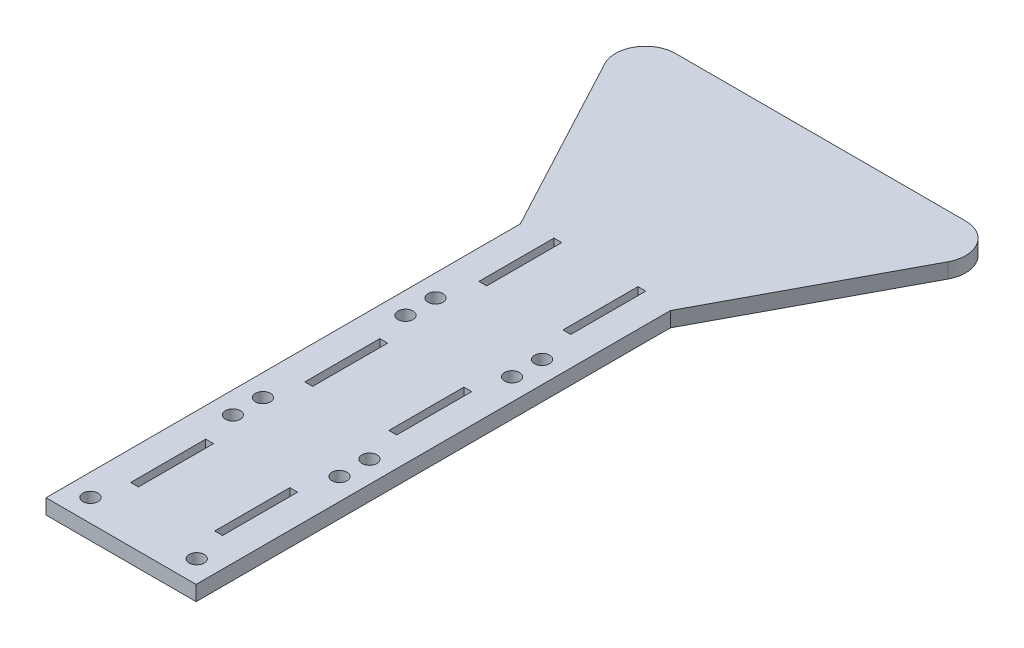
SolidWorks part; units mm, degrees
material "PC High Viscosity"
ref_plane "Front" through (0, 0, 0) normal (0, 0, 1) x (1, 0, 0)
ref_plane "Top" through (0, 0, 0) normal (0, 1, 0) x (1, 0, 0)
ref_plane "Right" through (0, 0, 0) normal (1, 0, 0) x (0, 0, -1)
sketch "Sketch1" plane through (0, 0, 0) normal (0, 1, 0) x (1, 0, 0)
  line L0 (-31.75, 0) -> (31.75, 0)
  line L1 (31.75, 0) -> (31.75, 200.66)
  line L2 (31.75, 200.66) -> (82.55, 295.91)
  line L3 (82.55, 295.91) -> (-82.55, 295.91)
  line L4 (-82.55, 295.91) -> (-31.75, 200.66)
  line L5 (-31.75, 200.66) -> (-31.75, 0)
  point P4 (0, 0)
  dimension "D1" = 63.5
  dimension "D2" = 200.66
  dimension "D3" = 95.25
  dimension "D4" = 165.1
extrude "Boss-Extrude1" add sketch "Sketch1" along normal blind 6.35
sketch "Sketch2" plane through (0, 6.35, 0) normal (0, 1, 0) x (1, 0, 0)
  line L0 (-19.3675, 199.39) -> (-19.3675, 173.99) construction
  line L1 (-19.3675, 173.99) -> (-16.1925, 173.99) construction
  line L2 (-16.1925, 173.99) -> (-16.1925, 199.39) construction
  line L3 (-16.1925, 199.39) -> (-19.3675, 199.39) construction
  line L4 (-19.3675, 125.73) -> (-19.3675, 100.33) construction
  line L5 (-19.3675, 100.33) -> (-16.1925, 100.33) construction
  line L6 (-16.1925, 100.33) -> (-16.1925, 125.73) construction
  line L7 (-16.1925, 125.73) -> (-19.3675, 125.73) construction
  line L12 (-19.3675, 52.07) -> (-19.3675, 26.67) construction
  line L13 (-19.3675, 26.67) -> (-16.1925, 26.67) construction
  line L14 (-16.1925, 26.67) -> (-16.1925, 52.07) construction
  line L15 (-16.1925, 52.07) -> (-19.3675, 52.07) construction
  line L20 (-19.3675, 199.39) -> (-19.3675, 173.99) construction
  line L21 (-19.3675, 173.99) -> (-16.1925, 173.99) construction
  line L22 (-16.1925, 173.99) -> (-16.1925, 199.39) construction
  line L23 (-16.1925, 199.39) -> (-19.3675, 199.39) construction
  line L24 (-19.3675, 125.73) -> (-19.3675, 100.33) construction
  line L25 (-19.3675, 100.33) -> (-16.1925, 100.33) construction
  line L26 (-16.1925, 100.33) -> (-16.1925, 125.73) construction
  line L27 (-16.1925, 125.73) -> (-19.3675, 125.73) construction
  line L32 (-19.3675, 52.07) -> (-19.3675, 26.67) construction
  line L33 (-19.3675, 26.67) -> (-16.1925, 26.67) construction
  line L34 (-16.1925, 26.67) -> (-16.1925, 52.07) construction
  line L35 (-16.1925, 52.07) -> (-19.3675, 52.07) construction
  line L36 (16.1925, 52.07) -> (16.1925, 26.67) construction
  line L37 (16.1925, 26.67) -> (19.3675, 26.67) construction
  line L38 (19.3675, 26.67) -> (19.3675, 52.07) construction
  line L39 (19.3675, 52.07) -> (16.1925, 52.07) construction
  line L44 (16.1925, 125.73) -> (16.1925, 100.33) construction
  line L45 (16.1925, 100.33) -> (19.3675, 100.33) construction
  line L46 (19.3675, 100.33) -> (19.3675, 125.73) construction
  line L47 (19.3675, 125.73) -> (16.1925, 125.73) construction
  line L48 (16.1925, 199.39) -> (16.1925, 173.99) construction
  line L49 (16.1925, 173.99) -> (19.3675, 173.99) construction
  line L50 (19.3675, 173.99) -> (19.3675, 199.39) construction
  line L51 (19.3675, 199.39) -> (16.1925, 199.39) construction
  line L56 (16.1925, 52.07) -> (16.1925, 26.67) construction
  line L57 (16.1925, 26.67) -> (19.3675, 26.67) construction
  line L58 (19.3675, 26.67) -> (19.3675, 52.07) construction
  line L59 (19.3675, 52.07) -> (16.1925, 52.07) construction
  line L60 (16.1925, 125.73) -> (16.1925, 100.33) construction
  line L61 (16.1925, 100.33) -> (19.3675, 100.33) construction
  line L62 (19.3675, 100.33) -> (19.3675, 125.73) construction
  line L63 (19.3675, 125.73) -> (16.1925, 125.73) construction
  line L68 (16.1925, 199.39) -> (16.1925, 173.99) construction
  line L69 (16.1925, 173.99) -> (19.3675, 173.99) construction
  line L70 (19.3675, 173.99) -> (19.3675, 199.39) construction
  line L71 (19.3675, 199.39) -> (16.1925, 199.39) construction
  line L72 (-19.431, 23.495) -> (-19.3675, 26.67) construction
  line L73 (-19.431, 23.495) -> (-16.129, 23.495)
  line L74 (-19.431, 23.495) -> (-19.431, 55.245)
  line L75 (-19.431, 55.245) -> (-16.129, 55.245)
  line L76 (-16.129, 23.495) -> (-16.129, 55.245)
  line L77 (-19.431, 97.155) -> (-16.129, 97.155)
  line L78 (-19.431, 97.155) -> (-19.431, 128.905)
  line L79 (-19.431, 128.905) -> (-16.129, 128.905)
  line L80 (-16.129, 97.155) -> (-16.129, 128.905)
  line L81 (-19.431, 170.815) -> (-16.129, 170.815)
  line L82 (-19.431, 170.815) -> (-19.431, 202.565)
  line L83 (-19.431, 202.565) -> (-16.129, 202.565)
  line L84 (-16.129, 170.815) -> (-16.129, 202.565)
  line L85 (16.129, 23.495) -> (19.431, 23.495)
  line L86 (16.129, 23.495) -> (16.129, 55.245)
  line L87 (16.129, 55.245) -> (19.431, 55.245)
  line L88 (19.431, 23.495) -> (19.431, 55.245)
  line L89 (16.129, 97.155) -> (19.431, 97.155)
  line L90 (16.129, 97.155) -> (16.129, 128.905)
  line L91 (16.129, 128.905) -> (19.431, 128.905)
  line L92 (19.431, 97.155) -> (19.431, 128.905)
  line L93 (16.129, 170.815) -> (19.431, 170.815)
  line L94 (16.129, 170.815) -> (16.129, 202.565)
  line L95 (16.129, 202.565) -> (19.431, 202.565)
  line L96 (19.431, 170.815) -> (19.431, 202.565)
  line L97 (-16.1925, 52.07) -> (-16.129, 55.245) construction
  line L98 (-19.431, 97.155) -> (-19.3675, 100.33) construction
  line L99 (-16.1925, 125.73) -> (-16.129, 128.905) construction
  line L100 (-19.3675, 173.99) -> (-19.431, 170.815) construction
  line L101 (-16.1925, 199.39) -> (-16.129, 202.565) construction
  line L102 (16.1925, 199.39) -> (16.129, 202.565) construction
  line L103 (19.3675, 173.99) -> (19.431, 170.815) construction
  line L104 (16.1925, 125.73) -> (16.129, 128.905) construction
  line L105 (19.3675, 100.33) -> (19.431, 97.155) construction
  line L106 (16.1925, 52.07) -> (16.129, 55.245) construction
  line L107 (19.3675, 26.67) -> (19.431, 23.495) construction
  dimension "D1" = 3.302
  dimension "D2" = 31.75
extrude "Cut-Extrude1" cut sketch "Sketch2" against normal through all
sketch "Sketch3" plane through (0, 6.35, 0) normal (0, 1, 0) x (1, 0, 0)
  line L0 (0, 295.91) -> (0, 149.225) construction
  line L1 (82.55, 295.91) -> (-82.55, 295.91) construction
  line L2 (0, 149.225) -> (-31.75, 149.225) construction
  line L3 (-31.75, 200.66) -> (-31.75, 0) construction
  line L4 (-31.75, 76.2) -> (-12.3639, 76.2) construction
  line L6 (-19.3675, 128.27) -> (-19.3675, 171.45) construction
  line L9 (-31.75, 0) -> (31.75, 0) construction
  circle A0 centre (-22.5425, 155.575) radius 3.175
  circle A1 centre (-22.5425, 142.875) radius 3.175
  circle A2 centre (22.5425, 142.875) radius 3.175
  circle A3 centre (22.5425, 155.575) radius 3.175
  circle A10 centre (-22.479, 9.525) radius 3.175
  circle A12 centre (22.479, 9.525) radius 3.175
  circle A13 centre (-22.5425, 82.55) radius 3.175
  circle A15 centre (-22.5425, 69.85) radius 3.175
  circle A16 centre (22.5425, 69.85) radius 3.175
  circle A17 centre (22.5425, 82.55) radius 3.175
  point P26 (0, 0)
  dimension "D2" = 6.35
  dimension "D4" = 9.271
  dimension "D3" = 12.7
  dimension "D6" = 6.35
  dimension "D7" = 12.7
  dimension "D1" = 9.525
  dimension "D5" = 149.225
  dimension "D8" = 76.2
extrude "Cut-Extrude2" cut sketch "Sketch3" against normal through all
fillet "Fillet1" radius 12.7 2 edges at (82.55, 3.175, -295.91) (-82.55, 3.175, -295.91)
